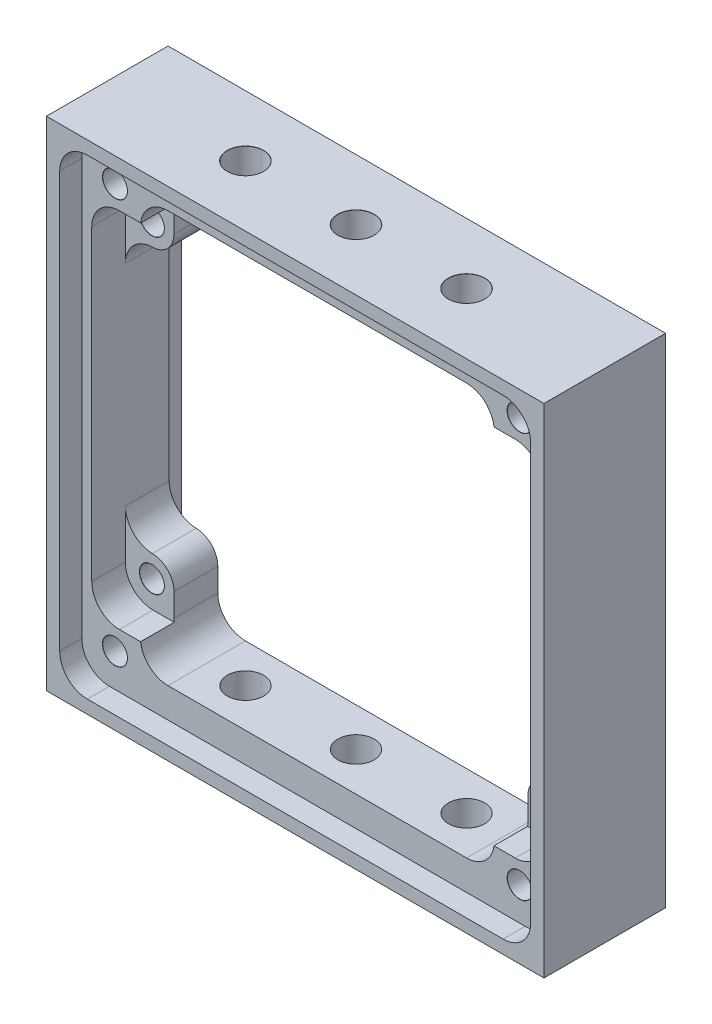
SolidWorks part; units mm, degrees
material "6061-T6 Al"
ref_plane "Front" through (0, 0, 0) normal (0, 0, 1) x (1, 0, 0)
ref_plane "Top" through (0, 0, 0) normal (0, 1, 0) x (1, 0, 0)
ref_plane "Right" through (0, 0, 0) normal (1, 0, 0) x (0, 0, -1)
sketch "Sketch1 w/mock PCB" plane through (0, 0, 0) normal (0, 0, 1) x (1, 0, 0)
  line L0 (-22.86, 17.78) -> (22.86, -17.78) construction
  line L1 (-28.575, 28.575) -> (28.575, 28.575)
  line L2 (-28.575, 28.575) -> (-28.575, -28.575)
  line L3 (-28.575, -28.575) -> (28.575, -28.575)
  line L4 (28.575, 28.575) -> (28.575, -28.575)
  line L6 (-28.575, -28.575) -> (28.575, 28.575) construction
  line L7 (-22.86, 20.32) -> (22.86, 20.32) construction
  line L8 (-25.4, 17.78) -> (-25.4, -17.78) construction
  line L9 (-22.86, -20.32) -> (22.86, -20.32) construction
  line L10 (25.4, 17.78) -> (25.4, -17.78) construction
  line L11 (-22.86, -17.78) -> (-22.86, 17.78) construction
  line L12 (-25.4, -20.32) -> (25.4, 20.32) construction
  line L13 (-22.86, 17.78) -> (22.86, 17.78) construction
  line L14 (25.908, 17.653) -> (25.908, 12.0664) construction
  line L15 (-22.733, -20.828) -> (-20.2971, -20.828) construction
  line L16 (-25.908, 17.653) -> (-25.908, 12.0664) construction
  line L17 (25.908, 20.828) -> (28.575, 23.495) construction
  line L18 (28.575, 0) -> (0, 0) construction
  line L19 (0, 0) -> (0, 28.575) construction
  line L21 (20.32, 17.78) -> (20.32, 20.447)
  line L22 (-20.32, 17.78) -> (-20.32, 20.447)
  line L23 (-20.32, -17.78) -> (-20.32, -20.447)
  line L24 (-17.145, -23.622) -> (17.145, -23.622)
  line L25 (-23.876, -27.051) -> (23.876, -27.051) construction
  line L26 (20.32, -17.78) -> (20.32, -20.447)
  line L27 (-23.876, 27.051) -> (23.876, 27.051) construction
  line L28 (27.051, 23.876) -> (27.051, -23.876) construction
  line L29 (-27.051, 23.876) -> (-27.051, -23.876) construction
  line L30 (-25.4, -27.051) -> (25.4, -27.051) construction
  line L31 (27.051, 20.701) -> (27.051, -20.701) construction
  line L32 (-22.733, 20.828) -> (-20.2971, 20.828) construction
  line L33 (-17.145, 23.622) -> (17.145, 23.622)
  line L34 (25.908, 12.0664) -> (25.908, -12.0664)
  line L35 (25.908, 20.701) -> (25.908, -20.701) construction
  line L36 (25.908, -12.0664) -> (25.908, -17.653) construction
  line L37 (-25.908, 12.0664) -> (-25.908, -12.0664)
  line L38 (-25.908, -12.0664) -> (-25.908, -17.653) construction
  line L39 (20.2971, 20.828) -> (22.733, 20.828) construction
  line L40 (20.2971, -20.828) -> (22.733, -20.828) construction
  line L41 (-25.4, -20.32) -> (25.4, -20.32) construction
  circle A0 centre (-22.86, 17.78) radius 1.4224 construction
  circle A1 centre (22.86, 17.78) radius 1.4224 construction
  circle A2 centre (-22.86, -17.78) radius 1.4224 construction
  circle A3 centre (22.86, -17.78) radius 1.4224 construction
  arc A9 (-22.8036, 15.2406) -> (-20.32, 17.78) centre (-22.86, 17.78) ccw
  arc A11 (-22.8036, 15.2406) -> (-25.908, 12.0664) centre (-22.733, 12.0664) ccw
  arc A13 (22.8036, 15.2406) -> (20.32, 17.78) centre (22.86, 17.78) cw
  arc A14 (22.8036, 15.2406) -> (25.908, 12.0664) centre (22.733, 12.0664) cw
  arc A15 (-22.8036, -15.2406) -> (-25.908, -12.0664) centre (-22.733, -12.0664) cw
  arc A16 (22.8036, -15.2406) -> (25.908, -12.0664) centre (22.733, -12.0664) ccw
  arc A17 (-22.8036, -15.2406) -> (-20.32, -17.78) centre (-22.86, -17.78) cw
  arc A18 (22.8036, -15.2406) -> (20.32, -17.78) centre (22.86, -17.78) ccw
  circle A21 centre (23.241, -23.241) radius 1.4224 construction
  circle A22 centre (-23.241, -23.241) radius 1.4224 construction
  circle A23 centre (23.241, 23.241) radius 1.4224 construction
  circle A24 centre (-23.241, 23.241) radius 1.4224 construction
  circle A25 centre (23.241, -23.241) radius 3.302 construction
  arc A26 (-27.051, -23.876) -> (-23.876, -27.051) centre (-23.876, -23.876) ccw construction
  arc A27 (23.876, -27.051) -> (27.051, -23.876) centre (23.876, -23.876) ccw construction
  arc A28 (23.876, 27.051) -> (27.051, 23.876) centre (23.876, 23.876) cw construction
  arc A29 (-23.876, 27.051) -> (-27.051, 23.876) centre (-23.876, 23.876) ccw construction
  arc A30 (-22.86, 20.32) -> (-25.4, 17.78) centre (-22.86, 17.78) ccw construction
  arc A31 (-25.4, -17.78) -> (-22.86, -20.32) centre (-22.86, -17.78) ccw construction
  arc A32 (22.86, -20.32) -> (25.4, -17.78) centre (22.86, -17.78) ccw construction
  arc A33 (25.4, 17.78) -> (22.86, 20.32) centre (22.86, 17.78) ccw construction
  arc A34 (22.733, 20.828) -> (25.908, 17.653) centre (22.733, 17.653) cw construction
  arc A35 (25.908, -17.653) -> (22.733, -20.828) centre (22.733, -17.653) cw construction
  arc A36 (-22.733, -20.828) -> (-25.908, -17.653) centre (-22.733, -17.653) cw construction
  arc A37 (-25.908, 17.653) -> (-22.733, 20.828) centre (-22.733, 17.653) cw construction
  circle A38 centre (22.86, -17.78) radius 2.7051 construction
  circle A39 centre (-23.241, 23.241) radius 3.302 construction
  circle A40 centre (-22.86, 17.78) radius 2.7051 construction
  arc A41 (20.32, 20.447) -> (17.145, 23.622) centre (17.145, 20.447) ccw
  arc A42 (-17.145, 23.622) -> (-20.32, 20.447) centre (-17.145, 20.447) ccw
  arc A43 (-17.145, -23.622) -> (-20.32, -20.447) centre (-17.145, -20.447) cw
  arc A44 (20.32, -20.447) -> (17.145, -23.622) centre (17.145, -20.447) cw
  point P5 (-25.908, 20.828)
  point P7 (25.908, -20.828)
  point P8 (-25.908, -20.828)
  point P37 (-25.4, 20.32)
  point P63 (-25.781, -19.05)
  point P64 (25.781, -19.05)
  dimension "D5" = 2.8448
  dimension "D6" = 0.508
  dimension "D7" = 35.56
  dimension "D8" = 45
  dimension "D9" = 3.175
  dimension "D10" = 2.54
  dimension "D12" = 3.81
  dimension "D13" = 6.604
  dimension "D16" = 1.524
  dimension "D19" = 3.81
  dimension "D22" = 2.54
  dimension "D23" = 5.4102
  dimension "D14" = 0.508
  dimension "D1" = 50.8
  dimension "D2" = 57.15
  dimension "D3" = 40.64
  dimension "D4" = 45.72
  dimension "D15" = 1.143
  dimension "D17" = 47.244
  dimension "D18" = 57.15
  dimension "D20" = 46.482
  dimension "D21" = 46.482
  dimension "D11" = 1.143
extrude "Boss-Extrude1" add sketch "Sketch1 w/mock PCB" along normal mid plane 13.97
sketch "Sketch2" plane through (0, 0, 6.985) normal (0, 0, 1) x (1, 0, 0)
  line L0 (-23.876, 27.051) -> (23.876, 27.051) construction
  line L1 (-27.051, 23.876) -> (-27.051, -23.876) construction
  line L2 (-23.876, -27.051) -> (23.876, -27.051) construction
  line L3 (27.051, 23.876) -> (27.051, -23.876) construction
  line L6 (-23.876, 27.051) -> (23.876, 27.051)
  line L7 (-27.051, 23.876) -> (-27.051, -23.876)
  line L8 (-23.876, -27.051) -> (23.876, -27.051)
  line L9 (27.051, 23.876) -> (27.051, -23.876)
  arc A0 (27.051, 23.876) -> (23.876, 27.051) centre (23.876, 23.876) ccw construction
  arc A1 (-23.876, 27.051) -> (-27.051, 23.876) centre (-23.876, 23.876) ccw construction
  arc A2 (-27.051, -23.876) -> (-23.876, -27.051) centre (-23.876, -23.876) ccw construction
  arc A3 (23.876, -27.051) -> (27.051, -23.876) centre (23.876, -23.876) ccw construction
  arc A5 (27.051, 23.876) -> (23.876, 27.051) centre (23.876, 23.876) ccw
  arc A6 (-23.876, 27.051) -> (-27.051, 23.876) centre (-23.876, 23.876) ccw
  arc A7 (-27.051, -23.876) -> (-23.876, -27.051) centre (-23.876, -23.876) ccw
  arc A8 (23.876, -27.051) -> (27.051, -23.876) centre (23.876, -23.876) ccw
extrude "Cut-Extrude1" cut sketch "Sketch2" against normal blind 2.54
mirror "Mirror1" about plane through (0, 0, 0) normal (0, 0, 1) of "Cut-Extrude1"
sketch "Sketch4" plane through (0, 0, 4.445) normal (0, 0, 1) x (1, 0, 0)
  line L0 (-20.32, 17.78) -> (-20.32, 20.447) construction
  line L1 (-25.908, 17.653) -> (-25.908, 12.0664) construction
  line L6 (-20.32, 17.78) -> (-20.32, 20.447)
  line L7 (25.908, -12.0664) -> (25.908, -17.653) construction
  line L13 (-25.908, -12.0664) -> (-25.908, -17.653) construction
  line L14 (-25.908, 17.653) -> (-25.908, 12.0664)
  line L15 (-22.733, 20.828) -> (-20.2971, 20.828) construction
  line L17 (20.2971, 20.828) -> (22.733, 20.828) construction
  line L18 (25.908, -12.0664) -> (25.908, -17.653)
  line L20 (20.32, -17.78) -> (20.32, -20.447) construction
  line L21 (-25.908, -12.0664) -> (-25.908, -17.653)
  line L22 (25.908, 17.653) -> (25.908, 12.0664) construction
  line L23 (20.32, 17.78) -> (20.32, 20.447) construction
  line L24 (20.2971, -20.828) -> (22.733, -20.828) construction
  line L25 (20.32, -17.78) -> (20.32, -20.447)
  line L26 (20.2971, -20.828) -> (22.733, -20.828)
  line L27 (-20.32, -17.78) -> (-20.32, -20.447) construction
  line L28 (-22.733, -20.828) -> (-20.2971, -20.828) construction
  line L29 (-20.32, -17.78) -> (-20.32, -20.447)
  line L30 (-22.733, -20.828) -> (-20.2971, -20.828)
  line L31 (-22.733, 20.828) -> (-20.2971, 20.828)
  line L32 (20.2971, 20.828) -> (22.733, 20.828)
  line L33 (25.908, 17.653) -> (25.908, 12.0664)
  line L34 (20.32, 17.78) -> (20.32, 20.447)
  arc A0 (-17.145, 23.622) -> (-20.32, 20.447) centre (-17.145, 20.447) ccw construction
  arc A4 (-22.733, 20.828) -> (-25.908, 17.653) centre (-22.733, 17.653) ccw construction
  arc A7 (-20.2971, 20.828) -> (-20.32, 20.447) centre (-17.145, 20.447) ccw
  arc A14 (22.8036, -15.2406) -> (25.908, -12.0664) centre (22.733, -12.0664) ccw construction
  arc A17 (-25.908, -17.653) -> (-22.733, -20.828) centre (-22.733, -17.653) ccw construction
  arc A20 (-22.8036, 15.2406) -> (-20.32, 17.78) centre (-22.86, 17.78) ccw construction
  arc A21 (-25.908, -12.0664) -> (-22.8036, -15.2406) centre (-22.733, -12.0664) ccw construction
  arc A24 (-22.8036, 15.2406) -> (-25.908, 12.0664) centre (-22.733, 12.0664) ccw construction
  arc A25 (-22.8036, 15.2406) -> (-20.32, 17.78) centre (-22.86, 17.78) ccw
  arc A26 (-22.8036, 15.2406) -> (-25.908, 12.0664) centre (-22.733, 12.0664) ccw
  arc A28 (20.32, 20.447) -> (17.145, 23.622) centre (17.145, 20.447) ccw construction
  arc A30 (-22.733, 20.828) -> (-25.908, 17.653) centre (-22.733, 17.653) ccw
  arc A32 (22.8036, -15.2406) -> (25.908, -12.0664) centre (22.733, -12.0664) ccw
  arc A33 (22.8036, -15.2406) -> (20.32, -17.78) centre (22.86, -17.78) ccw construction
  arc A35 (-25.908, -17.653) -> (-22.733, -20.828) centre (-22.733, -17.653) ccw
  arc A36 (-20.32, -17.78) -> (-22.8036, -15.2406) centre (-22.86, -17.78) ccw construction
  arc A38 (-25.908, -12.0664) -> (-22.8036, -15.2406) centre (-22.733, -12.0664) ccw
  arc A39 (-20.32, -20.447) -> (-17.145, -23.622) centre (-17.145, -20.447) ccw construction
  arc A41 (25.908, 17.653) -> (22.733, 20.828) centre (22.733, 17.653) ccw construction
  arc A42 (25.908, 12.0664) -> (22.8036, 15.2406) centre (22.733, 12.0664) ccw construction
  arc A43 (20.32, 17.78) -> (22.8036, 15.2406) centre (22.86, 17.78) ccw construction
  arc A44 (20.32, 20.447) -> (20.2971, 20.828) centre (17.145, 20.447) ccw
  arc A45 (22.733, -20.828) -> (25.908, -17.653) centre (22.733, -17.653) ccw construction
  arc A46 (22.8036, -15.2406) -> (20.32, -17.78) centre (22.86, -17.78) ccw
  arc A47 (17.145, -23.622) -> (20.32, -20.447) centre (17.145, -20.447) ccw construction
  arc A48 (22.733, -20.828) -> (25.908, -17.653) centre (22.733, -17.653) ccw
  arc A49 (20.2971, -20.828) -> (20.32, -20.447) centre (17.145, -20.447) ccw
  arc A50 (-20.32, -17.78) -> (-22.8036, -15.2406) centre (-22.86, -17.78) ccw
  arc A51 (-20.32, -20.447) -> (-20.2971, -20.828) centre (-17.145, -20.447) ccw
  arc A52 (25.908, 17.653) -> (22.733, 20.828) centre (22.733, 17.653) ccw
  arc A53 (25.908, 12.0664) -> (22.8036, 15.2406) centre (22.733, 12.0664) ccw
  arc A54 (20.32, 17.78) -> (22.8036, 15.2406) centre (22.86, 17.78) ccw
extrude "Cut-Extrude3" cut sketch "Sketch4" against normal offset from surface (3.8608 mm away) 5.0292 up to face at (0, 0, -4.445)
hole_wizard "#4-40 Tapped Hole1" positions "Sketch12" profile "Sketch11" tap size "#4-40" standard "ANSI Inch" end condition up to next
sketch "Sketch12" plane through (-22.2284, 15.4665, 0.5842) normal (0, 0, 1) x (1, 0, 0)
  point P0 (45.0884, 2.3135)
  point P3 (-0.6316, 2.3135)
  point P6 (45.0884, -33.2465)
  point P9 (-0.6316, -33.2465)
sketch "Sketch11" plane through (22.86, 17.78, 0.5842) normal (1, 0, 0) x (0, -1, 0)
  line L0 (0, 0) -> (0, 5.0292)
  line L1 (0, 5.0292) -> (1.4351, 5.0292)
  line L2 (1.4224, 5.0165) -> (1.4224, 0.0127)
  line L3 (1.4224, 0.0127) -> (1.4351, 0)
  line L5 (1.4351, 0) -> (0, 0)
  line L6 (-1.4224, 0.0127) -> (-1.4351, 0) construction
  line L7 (1.4351, 5.0292) -> (1.4224, 5.0165)
  line L8 (-1.4351, 5.0292) -> (-1.4224, 5.0165) construction
  line L11 (0, -6.35) -> (0, 107.95) construction
  dimension "Thread Major Dia." = 2.8448
  dimension "Thru Tap Drill Depth" = 5.0292
  dimension "Near C'Sink Dia." = 2.8702
  dimension "Near C'Sink Angle" = 90
  dimension "Far C'Sink Dia." = 2.8702
  dimension "Far C'Sink Angle" = 90
hole_wizard "#4-40 Tapped Hole2" positions "Sketch23" profile "Sketch22" tap size "#4-40" standard "ANSI Inch" end condition through all
sketch "Sketch23" plane through (0, 0, 4.445) normal (0, 0, 1) x (1, 0, 0)
  point P0 (-23.241, 23.241)
  point P3 (23.241, 23.241)
  point P6 (23.241, -23.241)
  point P9 (-23.241, -23.241)
sketch "Sketch22" plane through (-23.241, 23.241, 4.445) normal (1, 0, 0) x (0, -1, 0)
  line L0 (0, 0) -> (0, 8.89)
  line L1 (0, 8.89) -> (1.4351, 8.89)
  line L2 (1.4224, 8.8773) -> (1.4224, 0.0127)
  line L3 (1.4224, 0.0127) -> (1.4351, 0)
  line L5 (1.4351, 0) -> (0, 0)
  line L6 (-1.4224, 0.0127) -> (-1.4351, 0) construction
  line L7 (1.4351, 8.89) -> (1.4224, 8.8773)
  line L8 (-1.4351, 8.89) -> (-1.4224, 8.8773) construction
  line L11 (0, -6.35) -> (0, 107.95) construction
  dimension "Thread Major Dia." = 2.8448
  dimension "Thru Tap Drill Depth" = 8.89
  dimension "Near C'Sink Dia." = 2.8702
  dimension "Near C'Sink Angle" = 90
  dimension "Far C'Sink Dia." = 2.8702
  dimension "Far C'Sink Angle" = 90
hole_wizard "#8-32 Tapped Hole1" positions "3DSketch1" profile "Sketch15" tap size "#8-32" standard "ANSI Inch" end condition up to next
sketch3d "3DSketch1"
  line L6 (28.575, 28.575, 6.985) -> (-28.575, 28.575, 6.985) construction
  line L7 (12.7, 28.575, 0) -> (17.145, 23.622, 0) construction
  line L8 (17.145, 23.622, 4.445) -> (17.145, 23.622, -4.445) construction
  point P11 (-12.7, 28.575, 0)
  point P13 (12.7, 28.575, 0)
  point P15 (0, 28.575, 0)
  point P19 (12.7, -28.575, 0)
  point P21 (0, -28.575, 0)
  point P23 (-12.7, -28.575, 0)
  dimension "D1" = 6.985
  dimension "D2" = 25.4
sketch "Sketch15" plane through (-12.7, 28.575, 0) normal (1, 0, 0) x (0, 0, 1)
  line L0 (0, 0) -> (0, 4.953)
  line L1 (0, 4.953) -> (2.0828, 4.953)
  line L2 (2.0828, 4.953) -> (2.0828, 0.0127)
  line L3 (2.0828, 0.0127) -> (2.0955, 0)
  line L5 (2.0955, 0) -> (0, 0)
  line L6 (-2.0828, 0.0127) -> (-2.0955, 0) construction
  line L11 (0, -6.35) -> (0, 107.95) construction
  dimension "Thread Major Dia." = 4.1656
  dimension "Thru Tap Drill Depth" = 4.953
  dimension "Near C'Sink Dia." = 4.191
  dimension "Near C'Sink Angle" = 90
